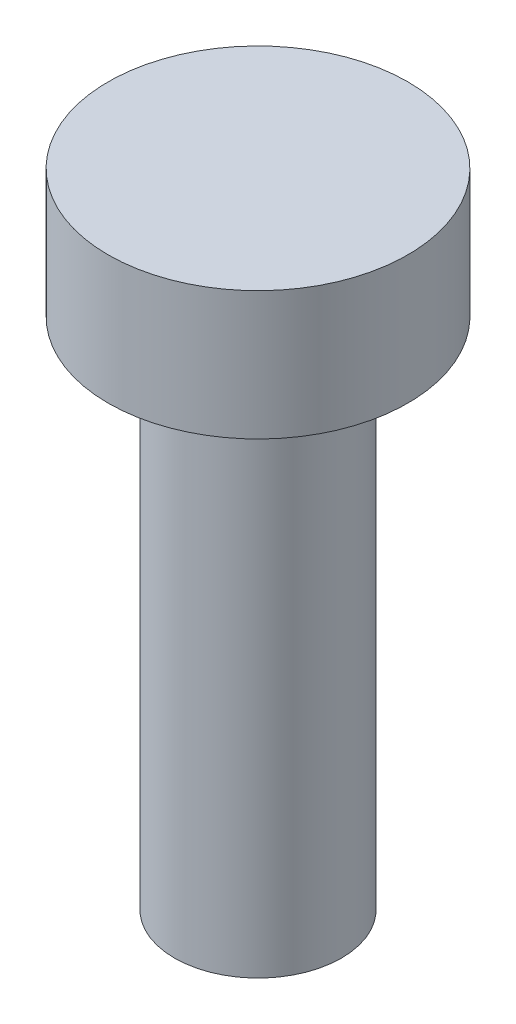
SolidWorks part; units mm, degrees
ref_plane "Front Plane" through (0, 0, 0) normal (0, 0, 1) x (1, 0, 0)
ref_plane "Top Plane" through (0, 0, 0) normal (0, 1, 0) x (1, 0, 0)
ref_plane "Right Plane" through (0, 0, 0) normal (1, 0, 0) x (0, 0, -1)
sketch "Sketch1" plane through (0, 0, 0) normal (0, 1, 0) x (1, 0, 0)
  circle A0 centre (0, 0) radius 3.5
  dimension "D1" = 7
extrude "Boss-Extrude1" add sketch "Sketch1" along normal blind 3
sketch "Sketch2" plane through (0, 0, 0) normal (0, -1, 0) x (1, 0, 0)
  circle A0 centre (0, 0) radius 1.95
  dimension "D1" = 3.9
extrude "Boss-Extrude2" add sketch "Sketch2" along normal blind 12
